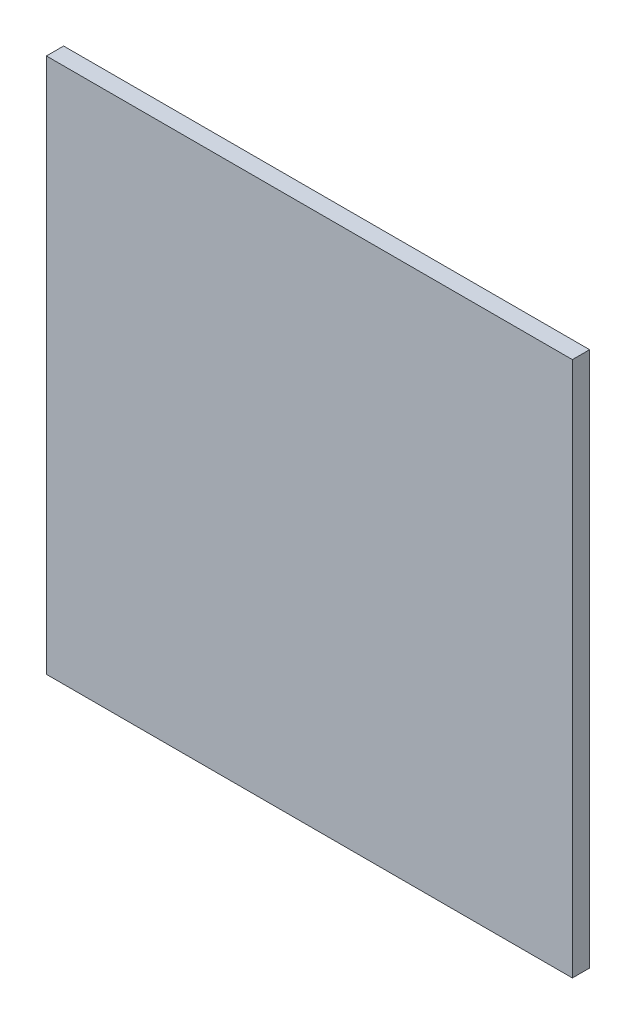
SolidWorks part; units mm, degrees
ref_plane "Front Plane" through (0, 0, 0) normal (0, 0, 1) x (1, 0, 0)
ref_plane "Top Plane" through (0, 0, 0) normal (0, 1, 0) x (1, 0, 0)
ref_plane "Right Plane" through (0, 0, 0) normal (1, 0, 0) x (0, 0, -1)
sketch "Sketch1" plane through (0, 0, 0) normal (0, 0, 1) x (1, 0, 0)
  line L1 (275, -280) -> (-275, -280)
  line L2 (275, -280) -> (275, 280)
  line L3 (275, 280) -> (-275, 280)
  line L4 (-275, -280) -> (-275, 280)
  line L5 (275, -280) -> (-275, 280) construction
  line L6 (275, 280) -> (-275, -280) construction
  point P0 (0, 0)
  dimension "D1" = 560
  dimension "D2" = 550
extrude "Boss-Extrude1" add sketch "Sketch1" along normal blind 18
equation "\"H_DSP\"=18"
equation "\"D1@Boss-Extrude1\"=\"H_DSP\""
